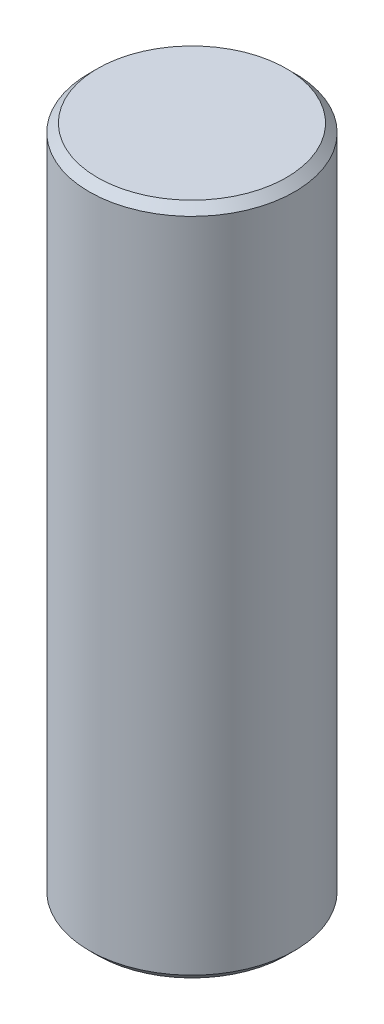
SolidWorks part; units mm, degrees
material "Gray Cast Iron (SN)"
ref_plane "Front Plane" through (0, 0, 0) normal (0, 0, 1) x (1, 0, 0)
ref_plane "Top Plane" through (0, 0, 0) normal (0, 1, 0) x (1, 0, 0)
ref_plane "Right Plane" through (0, 0, 0) normal (1, 0, 0) x (0, 0, -1)
sketch "Sketch1" plane through (0, 0, 0) normal (0, 1, 0) x (1, 0, 0)
  circle A0 centre (0, 0) radius 12.5
  dimension "D1" = 25
extrude "Boss-Extrude1" add sketch "Sketch1" along normal blind 82
chamfer "Chamfer2" distance 1 angle 45 2 edges at (0, 82, 12.5) (0, 0, 12.5)
